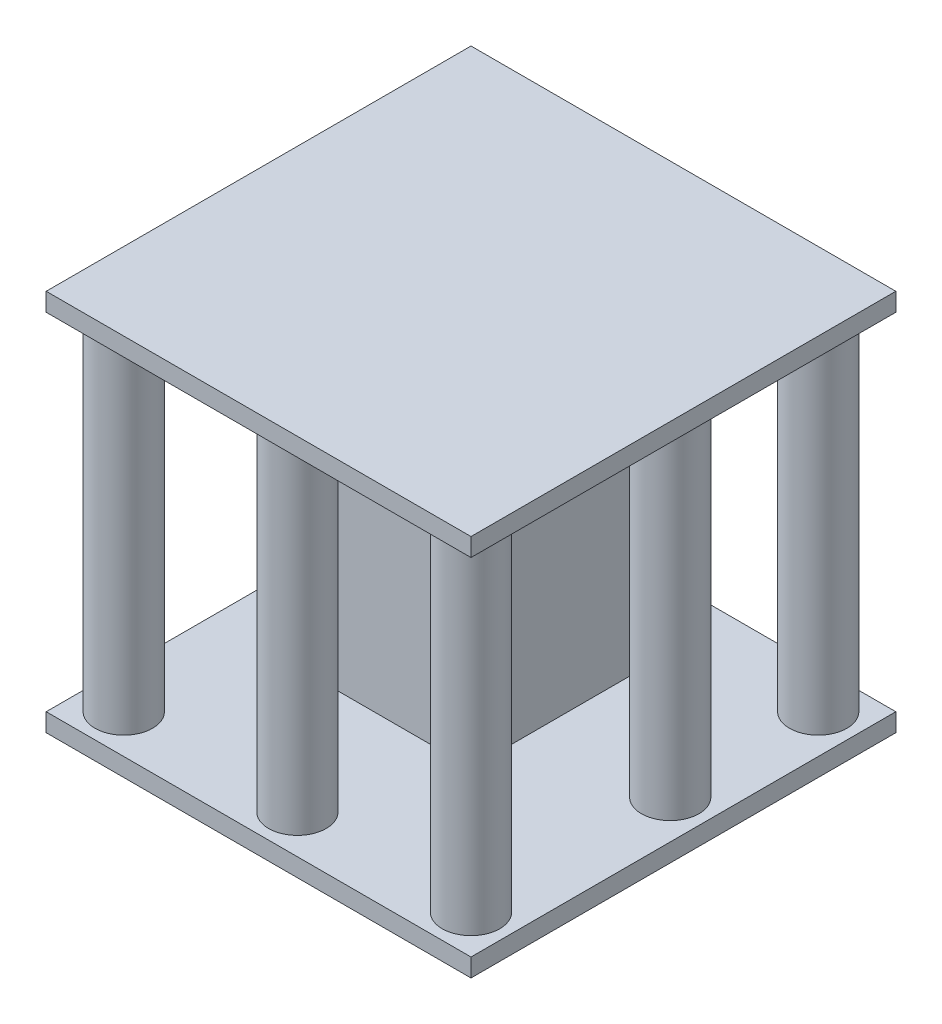
SolidWorks part; units mm, degrees
ref_plane "Front Plane" through (0, 0, 0) normal (0, 0, 1) x (1, 0, 0)
ref_plane "Top Plane" through (0, 0, 0) normal (0, 1, 0) x (1, 0, 0)
ref_plane "Right Plane" through (0, 0, 0) normal (1, 0, 0) x (0, 0, -1)
sketch "Sketch1" plane through (0, 0, 0) normal (0, 1, 0) x (1, 0, 0)
  line L1 (17.5, -17.5) -> (-17.5, -17.5)
  line L2 (17.5, -17.5) -> (17.5, 17.5)
  line L3 (17.5, 17.5) -> (-17.5, 17.5)
  line L4 (-17.5, -17.5) -> (-17.5, 17.5)
  line L5 (17.5, -17.5) -> (-17.5, 17.5) construction
  line L6 (17.5, 17.5) -> (-17.5, -17.5) construction
  line L7 (7.5, -7.5) -> (-7.5, -7.5)
  line L8 (7.5, -7.5) -> (7.5, 7.5)
  line L9 (7.5, 7.5) -> (-7.5, 7.5)
  line L10 (-7.5, -7.5) -> (-7.5, 7.5)
  line L11 (7.5, -7.5) -> (-7.5, 7.5) construction
  line L12 (7.5, 7.5) -> (-7.5, -7.5) construction
  circle A0 centre (-14.304, 14.304) radius 2.3696
  circle A1 centre (14.304, 14.304) radius 2.3696
  circle A2 centre (14.304, -14.304) radius 2.3696
  circle A3 centre (-14.304, -14.304) radius 2.3696
  circle A4 centre (-14.304, 0) radius 2.3696
  circle A5 centre (0, -14.304) radius 2.3696
  circle A6 centre (14.304, 2.111) radius 2.3696
  circle A7 centre (0, 14.304) radius 2.3696
  point P0 (0, 0)
  point P22 (0, 0)
  dimension "D1" = 35
  dimension "D2" = 35
  dimension "D3" = 15
  dimension "D4" = 15
sketch "Sketch5" plane through (0, 0, 0) normal (0, 1, 0) x (1, 0, 0)
  line L0 (17.5, 17.5) -> (-17.5, -17.5) construction
  circle A0 centre (-14.304, 14.304) radius 2.1537
  circle A1 centre (14.304, 14.304) radius 2.088
  circle A2 centre (14.304, -14.304) radius 1.9619
  circle A3 centre (-14.304, -14.304) radius 2.3696
sketch "Sketch9" plane through (0, 0, 0) normal (0, 1, 0) x (1, 0, 0)
  circle A0 centre (-14.304, 14.304) radius 2.3696
  circle A1 centre (14.304, 14.304) radius 2.3696
  circle A2 centre (14.304, -14.304) radius 2.3696
  circle A3 centre (-14.304, -14.304) radius 2.3696
  circle A4 centre (-14.304, 0) radius 2.3696
  circle A5 centre (0, -14.304) radius 2.3696
  circle A6 centre (14.304, 2.111) radius 2.3696
  circle A7 centre (0, 14.304) radius 2.3696
extrude "Boss-Extrude4" add sketch "Sketch9" along normal blind 30
sketch "Sketch10" plane through (0, 0, 0) normal (0, 1, 0) x (1, 0, 0)
  line L0 (7.5, -7.5) -> (-7.5, -7.5)
  line L1 (7.5, -7.5) -> (7.5, 7.5)
  line L2 (7.5, 7.5) -> (-7.5, 7.5)
  line L3 (-7.5, -7.5) -> (-7.5, 7.5)
extrude "Boss-Extrude5" add sketch "Sketch10" along normal blind 1 and the other way blind 15 from offset 20 separate body
sketch "Sketch11" plane through (0, 0, 0) normal (0, 1, 0) x (1, 0, 0)
  line L0 (17.5, -17.5) -> (-17.5, -17.5)
  line L1 (17.5, -17.5) -> (17.5, 17.5)
  line L2 (17.5, 17.5) -> (-17.5, 17.5)
  line L3 (-17.5, -17.5) -> (-17.5, 17.5)
extrude "Boss-Extrude6" add sketch "Sketch11" along normal blind 1.5
sketch "Sketch13" plane through (0, 0, 0) normal (0, 1, 0) x (1, 0, 0)
  line L0 (17.5, -17.5) -> (-17.5, -17.5)
  line L1 (17.5, -17.5) -> (17.5, 17.5)
  line L2 (17.5, 17.5) -> (-17.5, 17.5)
  line L3 (-17.5, -17.5) -> (-17.5, 17.5)
extrude "Boss-Extrude7" add sketch "Sketch13" along normal blind 1.5 from offset 30
